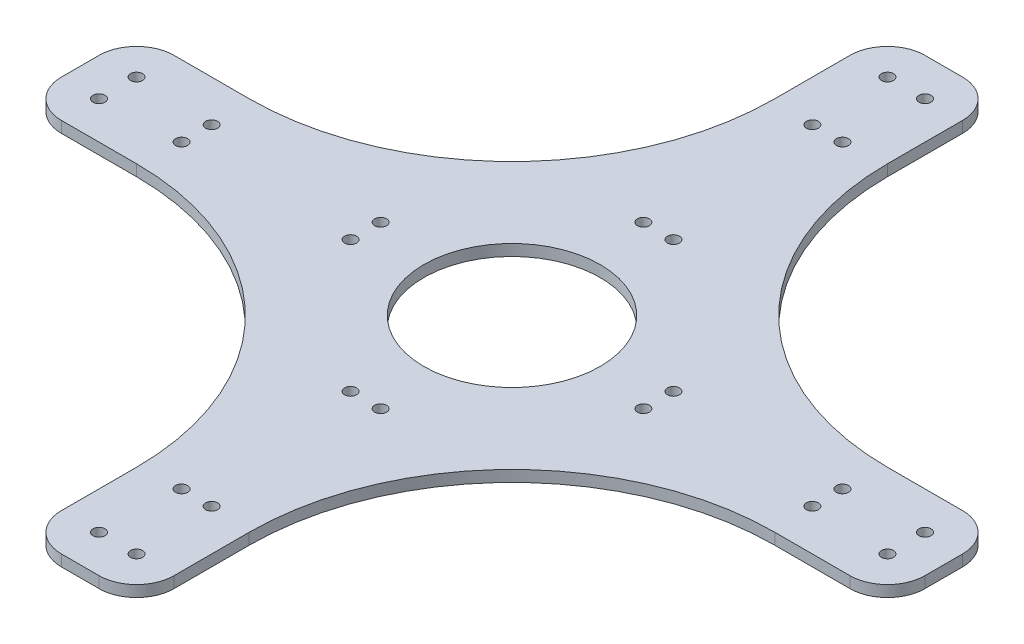
SolidWorks part; units mm, degrees
material "Thornel VCB-20 Carbon Cloth"
ref_plane "Front Plane" through (0, 0, 0) normal (0, 0, 1) x (1, 0, 0)
ref_plane "Top Plane" through (0, 0, 0) normal (0, 1, 0) x (1, 0, 0)
ref_plane "Right Plane" through (0, 0, 0) normal (1, 0, 0) x (0, 0, -1)
sketch "Sketch1" plane through (0, 0, 0) normal (0, 1, 0) x (1, 0, 0)
  line L0 (0, 115) -> (0, -115) construction
  line L1 (-115, 0) -> (115, 0) construction
  line L2 (85, 15) -> (105, 15)
  line L3 (5, 115) -> (-5, 115)
  line L4 (15, 105) -> (15, 85)
  line L5 (5, -115) -> (-5, -115)
  line L6 (-15, 105) -> (-15, 85)
  line L7 (-105, 15) -> (-85, 15)
  line L8 (-115, 5) -> (-115, -5)
  line L9 (-105, -15) -> (-85, -15)
  line L10 (115, 5) -> (115, -5)
  line L11 (15, -85) -> (15, -105)
  line L12 (85, -15) -> (105, -15)
  line L13 (-15, -85) -> (-15, -105)
  arc A0 (5, 115) -> (15, 105) centre (5, 105) cw
  arc A1 (-5, 115) -> (-15, 105) centre (-5, 105) ccw
  arc A2 (105, 15) -> (115, 5) centre (105, 5) cw
  arc A3 (105, -15) -> (115, -5) centre (105, -5) ccw
  arc A4 (15, -105) -> (5, -115) centre (5, -105) cw
  arc A5 (-5, -115) -> (-15, -105) centre (-5, -105) cw
  arc A6 (-115, -5) -> (-105, -15) centre (-105, -5) ccw
  arc A7 (-105, 15) -> (-115, 5) centre (-105, 5) ccw
  arc A8 (85, 15) -> (15, 85) centre (85, 85) cw
  arc A9 (15, -85) -> (85, -15) centre (85, -85) cw
  arc A10 (-85, -15) -> (-15, -85) centre (-85, -85) cw
  arc A11 (-15, 85) -> (-85, 15) centre (-85, 85) cw
  point P5 (0, 0)
  point P8 (0, 0)
  point P16 (0, 115)
  point P23 (15, 115)
  point P26 (-15, 115)
  point P43 (15, -15)
  point P46 (-15, -15)
  dimension "D1" = 30
  dimension "D3" = 10
  dimension "D4" = 70
  dimension "D2" = 230
extrude "Boss-Extrude1" add sketch "Sketch1" along normal mid plane 3
hole_wizard "M3 Clearance Hole1" positions "Sketch3" profile "Sketch4" hole size "M3" standard "ANSI Metric" end condition up to next
sketch "Sketch3" plane through (0, 1.5, 0) normal (0, 1, 0) x (1, 0, 0)
  point P0 (-105, 5)
  point P3 (-105, -5)
  point P6 (-5, 105)
  point P9 (5, 105)
  point P12 (105, 5)
  point P15 (105, -5)
  point P18 (5, -105)
  point P21 (-5, -105)
sketch "Sketch4" plane through (-105, 1.5, -5) normal (1, 0, 0) x (0, 0, 1)
  line L0 (0, 0) -> (0, 3)
  line L1 (0, 3) -> (1.6, 3)
  line L2 (1.6, 3) -> (1.6, 0)
  line L5 (1.6, 0) -> (0, 0)
  line L11 (0, -6.35) -> (0, 107.95) construction
  dimension "Thru Hole Dia." = 3.2
  dimension "Thru Hole Depth" = 3
sketch "Sketch5" plane through (0, 1.5, 0) normal (0, 1, 0) x (1, 0, 0)
  circle A0 centre (0, 0) radius 23.5
  dimension "D1" = 47
extrude "Cut-Extrude1" cut sketch "Sketch5" against normal through all both and the other way through all
sketch "Sketch7" plane through (0, -1.5, 0) normal (0, -1, 0) x (1, 0, 0)
  line L1 (39, 4) -> (84, 4)
  line L2 (39, 4) -> (39, -4)
  line L3 (39, -4) -> (84, -4)
  line L4 (84, 4) -> (84, -4)
  circle A0 centre (39, 4) radius 1.6
  circle A1 centre (39, -4) radius 1.6
  circle A2 centre (84, 4) radius 1.6
  circle A3 centre (84, -4) radius 1.6
  circle A4 centre (-4, -39) radius 1.6
  circle A5 centre (4, -39) radius 1.6
  circle A6 centre (4, -84) radius 1.6
  circle A7 centre (-4, -84) radius 1.6
  circle A8 centre (-39, 4) radius 1.6
  circle A9 centre (-39, -4) radius 1.6
  circle A10 centre (-84, -4) radius 1.6
  circle A11 centre (-84, 4) radius 1.6
  circle A12 centre (4, 39) radius 1.6
  circle A13 centre (-4, 39) radius 1.6
  circle A14 centre (-4, 84) radius 1.6
  circle A15 centre (4, 84) radius 1.6
  point P4 (39, 0)
  point P10 (0, 0)
  point P36 (0, 0)
  dimension "D4" = 3.2
  dimension "D1" = 45
  dimension "D2" = 8
  dimension "D3" = 39
  dimension "D5" = 4
extrude "Cut-Extrude2" cut sketch "Sketch7" against normal through all contours A1 | A0 | A2 | A3 | A5 | A4 | A7 | A6 | A9 | A8 | A11 | A10 | A14 | A15 | A12 | A13
